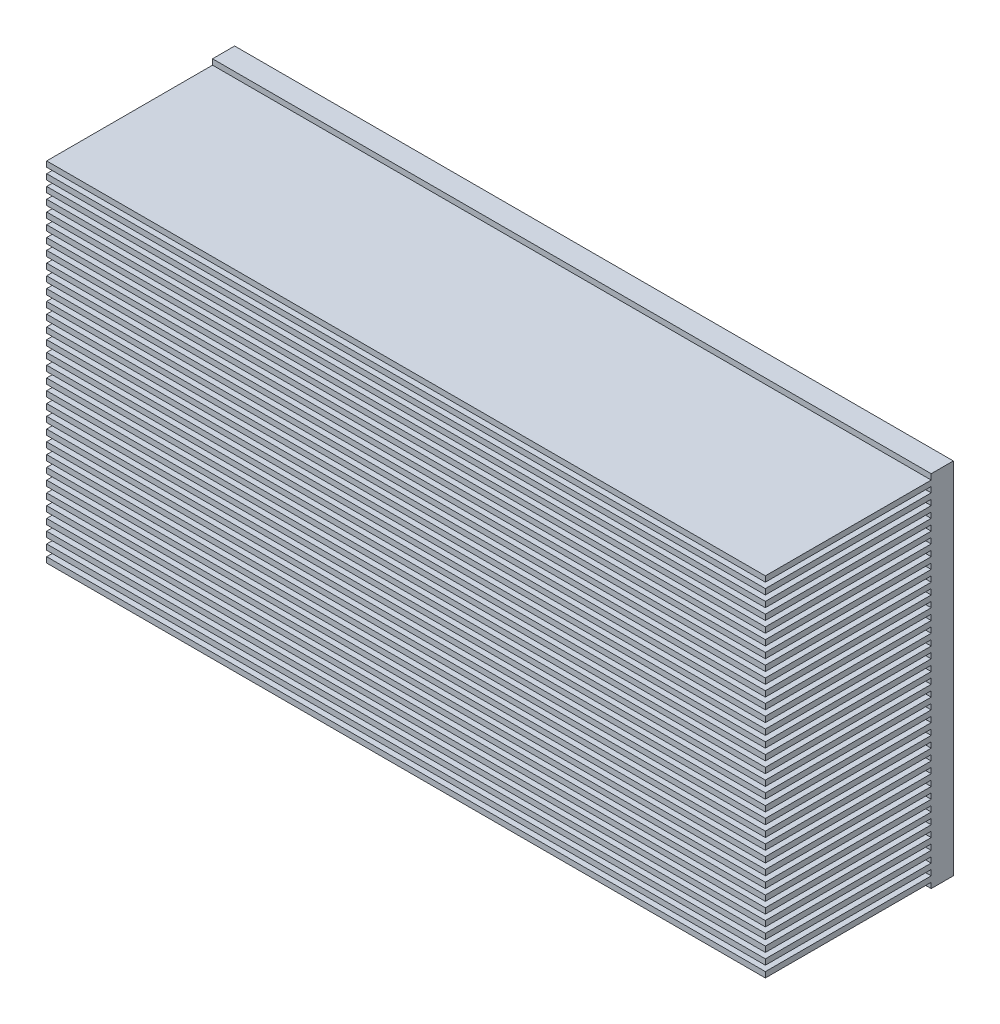
SolidWorks part; units mm, degrees
ref_plane "Plan de face" through (0, 0, 0) normal (0, 0, 1) x (1, 0, 0)
ref_plane "Plan de dessus" through (0, 0, 0) normal (0, 1, 0) x (1, 0, 0)
ref_plane "Plan de droite" through (0, 0, 0) normal (1, 0, 0) x (0, 0, -1)
sketch "Esquisse1" plane through (0, 0, 0) normal (0, 0, 1) x (1, 0, 0)
  line L1 (0, 0) -> (130, 0)
  line L2 (0, 0) -> (0, 65)
  line L3 (0, 65) -> (130, 65)
  line L4 (130, 0) -> (130, 65)
  dimension "D1" = 130
  dimension "D2" = 65
extrude "Boss.-Extru.1" add sketch "Esquisse1" along normal blind 4
sketch "Esquisse2" plane through (0, 0, 4) normal (0, 0, 1) x (1, 0, 0)
  line L0 (0, 65) -> (0, 0) construction
  line L1 (0, 2) -> (130, 2)
  line L2 (0, 2) -> (0, 1)
  line L3 (0, 1) -> (130, 1)
  line L4 (130, 2) -> (130, 1)
  line L5 (130, 0) -> (130, 65) construction
  line L6 (0, 0) -> (130, 0) construction
  line L7 (0, 4) -> (130, 4)
  line L8 (0, 4) -> (0, 3)
  line L9 (0, 3) -> (130, 3)
  line L10 (130, 4) -> (130, 3)
  line L11 (0, 6) -> (130, 6)
  line L12 (0, 6) -> (0, 5)
  line L13 (0, 5) -> (130, 5)
  line L14 (130, 6) -> (130, 5)
  line L15 (0, 8) -> (130, 8)
  line L16 (0, 8) -> (0, 7)
  line L17 (0, 7) -> (130, 7)
  line L18 (130, 8) -> (130, 7)
  line L19 (0, 10) -> (130, 10)
  line L20 (0, 10) -> (0, 9)
  line L21 (0, 9) -> (130, 9)
  line L22 (130, 10) -> (130, 9)
  line L23 (0, 12) -> (130, 12)
  line L24 (0, 12) -> (0, 11)
  line L25 (0, 11) -> (130, 11)
  line L26 (130, 12) -> (130, 11)
  line L27 (0, 14) -> (130, 14)
  line L28 (0, 14) -> (0, 13)
  line L29 (0, 13) -> (130, 13)
  line L30 (130, 14) -> (130, 13)
  line L31 (0, 16) -> (130, 16)
  line L32 (0, 16) -> (0, 15)
  line L33 (0, 15) -> (130, 15)
  line L34 (130, 16) -> (130, 15)
  line L35 (0, 18) -> (130, 18)
  line L36 (0, 18) -> (0, 17)
  line L37 (0, 17) -> (130, 17)
  line L38 (130, 18) -> (130, 17)
  line L39 (0, 20) -> (130, 20)
  line L40 (0, 20) -> (0, 19)
  line L41 (0, 19) -> (130, 19)
  line L42 (130, 20) -> (130, 19)
  line L43 (0, 22) -> (130, 22)
  line L44 (0, 22) -> (0, 21)
  line L45 (0, 21) -> (130, 21)
  line L46 (130, 22) -> (130, 21)
  line L47 (0, 24) -> (130, 24)
  line L48 (0, 24) -> (0, 23)
  line L49 (0, 23) -> (130, 23)
  line L50 (130, 24) -> (130, 23)
  line L51 (0, 26) -> (130, 26)
  line L52 (0, 26) -> (0, 25)
  line L53 (0, 25) -> (130, 25)
  line L54 (130, 26) -> (130, 25)
  line L55 (0, 28) -> (130, 28)
  line L56 (0, 28) -> (0, 27)
  line L57 (0, 27) -> (130, 27)
  line L58 (130, 28) -> (130, 27)
  line L59 (0, 30) -> (130, 30)
  line L60 (0, 30) -> (0, 29)
  line L61 (0, 29) -> (130, 29)
  line L62 (130, 30) -> (130, 29)
  line L63 (0, 32) -> (130, 32)
  line L64 (0, 32) -> (0, 31)
  line L65 (0, 31) -> (130, 31)
  line L66 (130, 32) -> (130, 31)
  line L67 (0, 34) -> (130, 34)
  line L68 (0, 34) -> (0, 33)
  line L69 (0, 33) -> (130, 33)
  line L70 (130, 34) -> (130, 33)
  line L71 (0, 36) -> (130, 36)
  line L72 (0, 36) -> (0, 35)
  line L73 (0, 35) -> (130, 35)
  line L74 (130, 36) -> (130, 35)
  line L75 (0, 38) -> (130, 38)
  line L76 (0, 38) -> (0, 37)
  line L77 (0, 37) -> (130, 37)
  line L78 (130, 38) -> (130, 37)
  line L79 (0, 40) -> (130, 40)
  line L80 (0, 40) -> (0, 39)
  line L81 (0, 39) -> (130, 39)
  line L82 (130, 40) -> (130, 39)
  line L83 (0, 42) -> (130, 42)
  line L84 (0, 42) -> (0, 41)
  line L85 (0, 41) -> (130, 41)
  line L86 (130, 42) -> (130, 41)
  line L87 (0, 44) -> (130, 44)
  line L88 (0, 44) -> (0, 43)
  line L89 (0, 43) -> (130, 43)
  line L90 (130, 44) -> (130, 43)
  line L91 (0, 46) -> (130, 46)
  line L92 (0, 46) -> (0, 45)
  line L93 (0, 45) -> (130, 45)
  line L94 (130, 46) -> (130, 45)
  line L95 (0, 48) -> (130, 48)
  line L96 (0, 48) -> (0, 47)
  line L97 (0, 47) -> (130, 47)
  line L98 (130, 48) -> (130, 47)
  line L99 (0, 50) -> (130, 50)
  line L100 (0, 50) -> (0, 49)
  line L101 (0, 49) -> (130, 49)
  line L102 (130, 50) -> (130, 49)
  line L103 (0, 52) -> (130, 52)
  line L104 (0, 52) -> (0, 51)
  line L105 (0, 51) -> (130, 51)
  line L106 (130, 52) -> (130, 51)
  line L107 (0, 54) -> (130, 54)
  line L108 (0, 54) -> (0, 53)
  line L109 (0, 53) -> (130, 53)
  line L110 (130, 54) -> (130, 53)
  line L111 (0, 56) -> (130, 56)
  line L112 (0, 56) -> (0, 55)
  line L113 (0, 55) -> (130, 55)
  line L114 (130, 56) -> (130, 55)
  line L115 (0, 58) -> (130, 58)
  line L116 (0, 58) -> (0, 57)
  line L117 (0, 57) -> (130, 57)
  line L118 (130, 58) -> (130, 57)
  line L119 (0, 60) -> (130, 60)
  line L120 (0, 60) -> (0, 59)
  line L121 (0, 59) -> (130, 59)
  line L122 (130, 60) -> (130, 59)
  line L123 (0, 62) -> (130, 62)
  line L124 (0, 62) -> (0, 61)
  line L125 (0, 61) -> (130, 61)
  line L126 (130, 62) -> (130, 61)
  line L127 (0, 64) -> (130, 64)
  line L128 (0, 64) -> (0, 63)
  line L129 (0, 63) -> (130, 63)
  line L130 (130, 64) -> (130, 63)
  dimension "D1" = 130
  dimension "D2" = 1
  dimension "D3" = 1
extrude "Boss.-Extru.2" add sketch "Esquisse2" along normal blind 30
sketch "Esquisse3" plane through (0, 0, 0) normal (0, 0, -1) x (-1, 0, 0)
  line L0 (0, 65) -> (0, 0) construction
  line L1 (-130, 65) -> (0, 65) construction
  line L2 (-5, 55) -> (-134.893, 55) construction
  line L3 (3.1098, 10) -> (-133.407, 10) construction
  line L4 (0, 0) -> (-130, 0) construction
  circle A0 centre (-5, 55) radius 1.6
  circle A1 centre (-29, 55) radius 1.6
  circle A2 centre (-53, 55) radius 1.6
  circle A3 centre (-77, 55) radius 1.6
  circle A4 centre (-101, 55) radius 1.6
  circle A5 centre (-125, 55) radius 1.6
  circle A6 centre (-5, 10) radius 1.6
  circle A7 centre (-29, 10) radius 1.6
  circle A8 centre (-53, 10) radius 1.6
  circle A9 centre (-77, 10) radius 1.6
  circle A10 centre (-101, 10) radius 1.6
  circle A11 centre (-125, 10) radius 1.6
  circle A12 centre (-40, 32.5) radius 1.6
  circle A13 centre (-90, 32.5) radius 1.6
  dimension "D1" = 24
  dimension "D9" = 32.5
  dimension "D2" = 24
  dimension "D3" = 5
  dimension "D4" = 24
  dimension "D5" = 24
  dimension "D6" = 24
  dimension "D7" = 10
  dimension "D8" = 10
  dimension "D10" = 32.5
  dimension "D11" = 40
  dimension "D12" = 50
extrude "Enlèv. mat.-Extru.5" cut sketch "Esquisse3" against normal blind 4
sketch "Esquisse5" plane through (0, 0, 34) normal (0, 0, 1) x (1, 0, 0)
  circle A0 centre (5, 55) radius 3
  circle A1 centre (29, 55) radius 3
  circle A2 centre (53, 55) radius 3
  circle A3 centre (77, 55) radius 3
  circle A4 centre (101, 55) radius 3
  circle A5 centre (125, 55) radius 3
  circle A6 centre (90, 32.5) radius 3
  circle A7 centre (40, 32.5) radius 3
  circle A8 centre (5, 10) radius 3
  circle A9 centre (29, 10) radius 3
  circle A10 centre (53, 10) radius 3
  circle A11 centre (77, 10) radius 3
  circle A12 centre (101, 10) radius 3
  circle A13 centre (125, 10) radius 3
